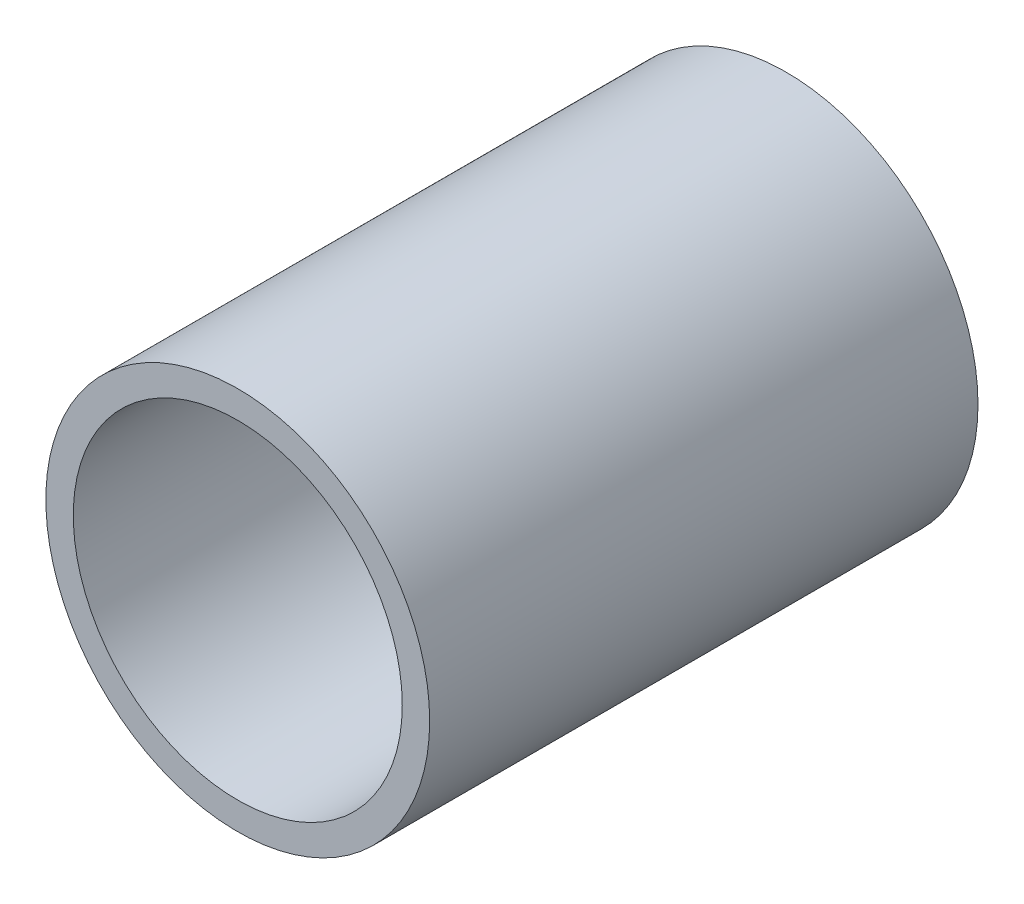
SolidWorks part; units mm, degrees
ref_plane "Front Plane" through (0, 0, 0) normal (0, 0, 1) x (1, 0, 0)
ref_plane "Top Plane" through (0, 0, 0) normal (0, 1, 0) x (1, 0, 0)
ref_plane "Right Plane" through (0, 0, 0) normal (1, 0, 0) x (0, 0, -1)
sketch "Sketch1" plane through (0, 0, 0) normal (0, 0, 1) x (1, 0, 0)
  circle A0 centre (0, 0) radius 60
  circle A1 centre (0, 0) radius 70
  dimension "D1" = 10
  dimension "D2" = 120
extrude "Boss-Extrude1" add sketch "Sketch1" along normal blind 200
